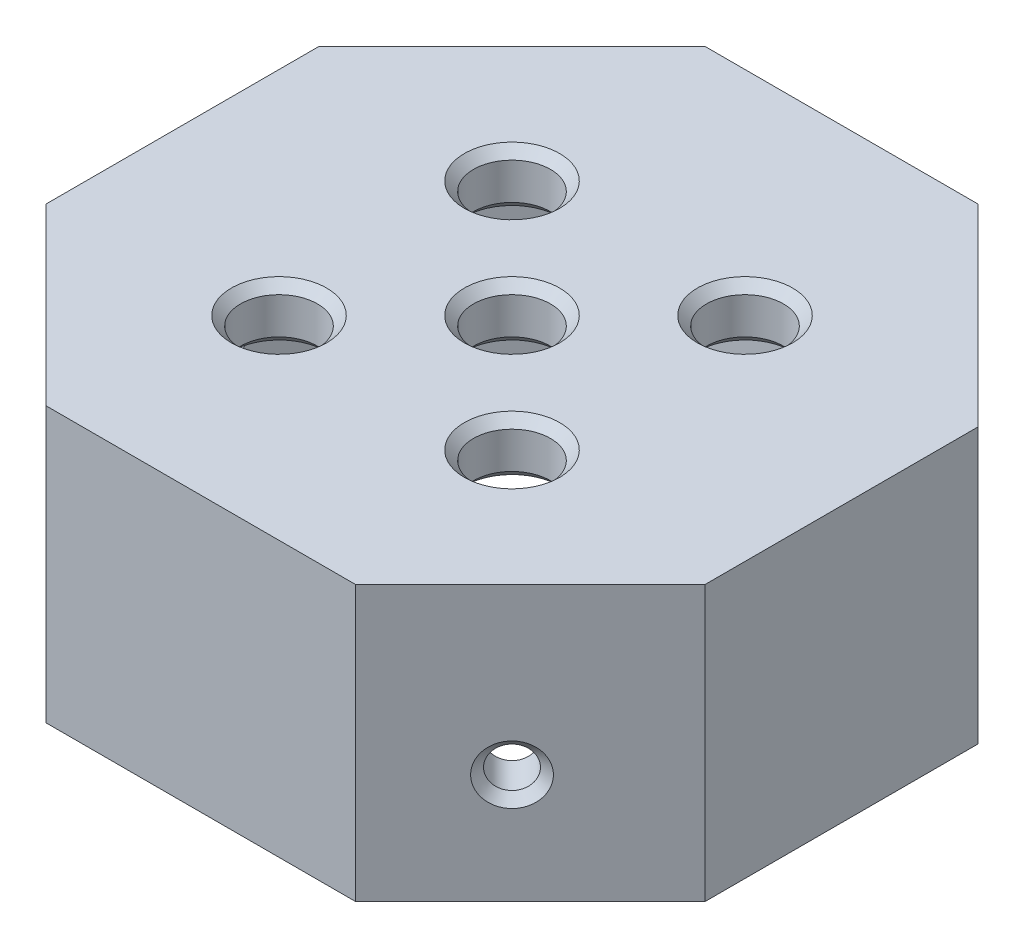
SolidWorks part; units mm, degrees
ref_plane "Спереди" through (0, 0, 0) normal (0, 0, 1) x (1, 0, 0)
ref_plane "Сверху" through (0, 0, 0) normal (0, 1, 0) x (1, 0, 0)
ref_plane "Справа" through (0, 0, 0) normal (1, 0, 0) x (0, 0, -1)
sketch "Эскиз1" plane through (0, 0, 0) normal (0, 1, 0) x (1, 0, 0)
  line L0 (0, 0) -> (0, 18) construction
  line L1 (-6.4203, 15.5) -> (-15.5, 6.4203)
  line L2 (-15.5, 6.4203) -> (-15.5, -6.4203)
  line L3 (-15.5, -6.4203) -> (-6.4203, -15.5)
  line L4 (-6.4203, -15.5) -> (6.4203, -15.5)
  line L5 (6.4203, -15.5) -> (15.5, -6.4203)
  line L6 (15.5, -6.4203) -> (15.5, 6.4203)
  line L7 (15.5, 6.4203) -> (6.4203, 15.5)
  line L8 (6.4203, 15.5) -> (-6.4203, 15.5)
  line L10 (-7.4558, 18) -> (-18, 7.4558)
  line L11 (-18, 7.4558) -> (-18, -7.4558)
  line L12 (-18, -7.4558) -> (-7.4558, -18)
  line L13 (-7.4558, -18) -> (7.4558, -18)
  line L14 (7.4558, -18) -> (18, -7.4558)
  line L15 (18, -7.4558) -> (18, 7.4558)
  line L16 (18, 7.4558) -> (7.4558, 18)
  line L17 (7.4558, 18) -> (-7.4558, 18)
  circle A0 centre (0, 0) radius 15.5 construction
  circle A1 centre (0, 0) radius 18 construction
  dimension "D1" = 31
  dimension "D2" = 2.5
extrude "Бобышка-Вытянуть1" add sketch "Эскиз1" along normal blind 12
sketch "Эскиз2" plane through (0, 12, 0) normal (0, 1, 0) x (1, 0, 0)
  line L8 (7.4558, 18) -> (-7.4558, 18)
  line L9 (-7.4558, 18) -> (-18, 7.4558)
  line L10 (-18, 7.4558) -> (-18, -7.4558)
  line L11 (-18, -7.4558) -> (-7.4558, -18)
  line L12 (-7.4558, -18) -> (7.4558, -18)
  line L13 (7.4558, -18) -> (18, -7.4558)
  line L14 (18, -7.4558) -> (18, 7.4558)
  line L15 (18, 7.4558) -> (7.4558, 18)
  line L16 (7.4558, 18) -> (-7.4558, 18)
  line L17 (-7.4558, 18) -> (-18, 7.4558)
  line L18 (-18, 7.4558) -> (-18, -7.4558)
  line L19 (-18, -7.4558) -> (-7.4558, -18)
  line L20 (-7.4558, -18) -> (7.4558, -18)
  line L21 (7.4558, -18) -> (18, -7.4558)
  line L22 (18, -7.4558) -> (18, 7.4558)
  line L23 (18, 7.4558) -> (7.4558, 18)
  dimension "D1" = 0
extrude "Бобышка-Вытянуть2" add sketch "Эскиз2" along normal blind 3
chamfer "Фаска1" distance 1 angle 45 8 edges at (-10.9602, 12, -10.9602) (-15.5, 12, 0) (-10.9602, 12, 10.9602) (0, 12, 15.5) (10.9602, 12, 10.9602) (15.5, 12, 0) (10.9602, 12, -10.9602) (0, 12, -15.5)
sketch "Эскиз3" plane through (0, 15, 0) normal (0, 1, 0) x (1, 0, 0)
  line L0 (0, -18) -> (0, 18) construction
  line L2 (-6.364, 6.364) -> (6.364, 6.364) construction
  line L3 (-6.364, 6.364) -> (-6.364, -6.364) construction
  line L4 (-6.364, -6.364) -> (6.364, -6.364) construction
  line L5 (-7.4558, -18) -> (7.4558, -18) construction
  line L6 (7.4558, 18) -> (-7.4558, 18) construction
  line L7 (6.364, 6.364) -> (6.364, -6.364) construction
  line L8 (-6.364, 6.364) -> (6.364, -6.364) construction
  line L9 (-6.364, -6.364) -> (6.364, 6.364) construction
  circle A0 centre (0, 0) radius 2.1
  circle A1 centre (-6.364, 6.364) radius 2.1
  circle A2 centre (6.364, 6.364) radius 2.1
  circle A3 centre (6.364, -6.364) radius 2.1
  circle A4 centre (-6.364, -6.364) radius 2.1
  circle A5 centre (0, 0) radius 9 construction
  point P8 (0, 0)
  dimension "D1" = 4.2
  dimension "D2" = 18
extrude "Вырез-Вытянуть1" cut sketch "Эскиз3" against normal through all
chamfer "Фаска3" distance 0.5 angle 45 5 edges at (0, 12, 2.1) (-6.364, 12, -4.264) (-6.364, 12, 8.464) (6.364, 12, 8.464) (6.364, 12, -4.264)
sketch "Эскиз4" plane through (-12.7279, 0, 12.7279) normal (-0.7071, 0, 0.7071) x (0.7071, 0, 0.7071)
  line L0 (0, 15) -> (0, 0) construction
  line L1 (-7.4558, 15) -> (7.4558, 15) construction
  line L2 (-7.4558, 0) -> (7.4558, 0) construction
  circle A0 centre (0, 6) radius 1.1
  point P8 (0, 7.5)
  dimension "D2" = 2.2
  dimension "D3" = 9
  dimension "D1" = 1.5
extrude "Вырез-Вытянуть2" cut sketch "Эскиз4" against normal through all
sketch "Эскиз5" plane through (12.7279, 0, 12.7279) normal (0.7071, 0, 0.7071) x (0.7071, 0, -0.7071)
  line L0 (0, 15) -> (0, 0) construction
  line L1 (-7.4558, 15) -> (7.4558, 15) construction
  line L2 (-7.4558, 0) -> (7.4558, 0) construction
  circle A0 centre (0, 6) radius 1.1
  dimension "D1" = 9
  dimension "D2" = 2.2
extrude "Вырез-Вытянуть3" cut sketch "Эскиз5" against normal through all
sketch "Эскиз6" plane through (-18, 0, 0) normal (-1, 0, 0) x (0, 0, 1)
  line L0 (0, 15) -> (0, 0) construction
  line L1 (-7.4558, 15) -> (7.4558, 15) construction
  line L2 (-7.4558, 0) -> (7.4558, 0) construction
  circle A0 centre (0, 6) radius 1.1
  dimension "D1" = 9
  dimension "D2" = 2.2
extrude "Вырез-Вытянуть4" cut sketch "Эскиз6" against normal up to surface (2.5 mm away) up to face at (-15.5, 5.5, 0)
chamfer "Фаска4" distance 0.5 angle 45 5 edges at (-11.9501, 6, 13.5057) (-18, 6, 1.1) (-11.9501, 6, -13.5057) (13.5057, 6, 11.9501) (13.5057, 6, -11.9501)
chamfer "Фаска5" distance 0.5 angle 45 5 edges at (-6.364, 15, -4.264) (6.364, 15, -4.264) (0, 15, 2.1) (6.364, 15, 8.464) (-6.364, 15, 8.464)
sketch "Эскиз9" plane through (0, 0, 0) normal (0, -1, 0) x (1, 0, 0)
  line L0 (-18, 7.4558) -> (-7.4558, 18) construction
  line L1 (-7.4558, 18) -> (7.4558, 18) construction
  line L2 (7.4558, 18) -> (18, 7.4558) construction
  line L3 (-8.4558, 17) -> (-7.4558, 18)
  line L4 (-7.4558, 18) -> (7.4558, 18)
  line L5 (7.4558, 18) -> (8.4558, 17)
  line L6 (-8.4558, 17) -> (8.4558, 17)
  dimension "D1" = 1
extrude "Вырез-Вытянуть5" cut sketch "Эскиз9" against normal through all
